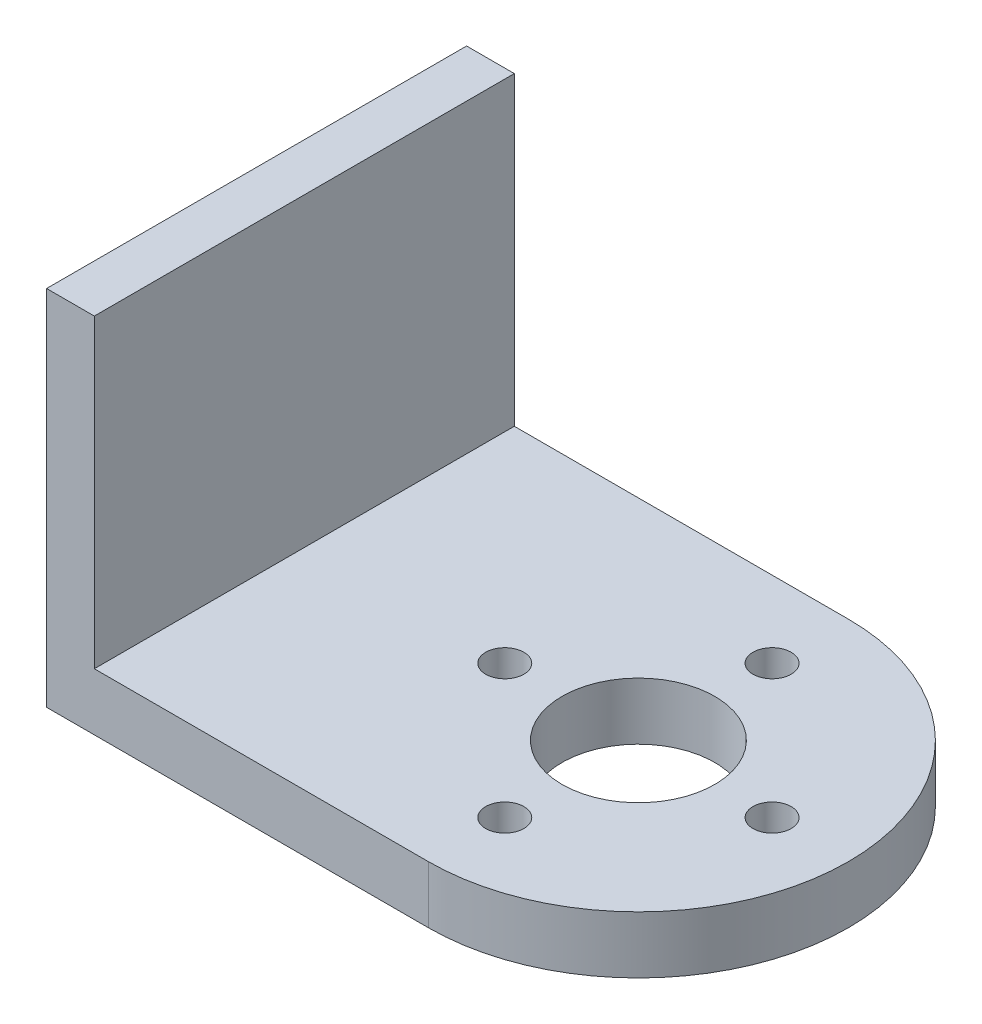
SolidWorks part; units mm, degrees
ref_plane "Front Plane" through (0, 0, 0) normal (0, 0, 1) x (1, 0, 0)
ref_plane "Top Plane" through (0, 0, 0) normal (0, 1, 0) x (1, 0, 0)
ref_plane "Right Plane" through (0, 0, 0) normal (1, 0, 0) x (0, 0, -1)
sketch "Sketch1" plane through (0, 0, 0) normal (0, 1, 0) x (1, 0, 0)
  line L0 (-28.2208, 0) -> (26.2745, 0) construction
  line L2 (-14, -11) -> (-14, 11)
  line L5 (-14, 11) -> (6, 11)
  line L6 (6, -11) -> (-14, -11)
  circle A0 centre (6, -7) radius 1
  circle A1 centre (-1, 0) radius 1
  circle A2 centre (6, 0) radius 4
  arc A3 (6, -11) -> (6, 11) centre (6, 0) ccw
  circle A4 centre (13, 0) radius 1
  circle A5 centre (6, 7) radius 1
  point P0 (0, 0)
  point P6 (-14, 0)
  point P22 (6, 0)
  dimension "D3" = 8
  dimension "D5" = 22
  dimension "D6" = 4
  dimension "D12" = 2
  dimension "D2" = 22
  dimension "D4" = 20
  dimension "D11" = 7
extrude "Boss-Extrude1" add sketch "Sketch1" along normal blind 3
sketch "Sketch2" plane through (0, 3, 0) normal (0, 1, 0) x (1, 0, 0)
  line L0 (-14, 11) -> (-11.5, 11)
  line L1 (6, 11) -> (-14, 11) construction
  line L2 (-11.5, 11) -> (-11.5, -11)
  line L3 (-14, -11) -> (6, -11) construction
  line L4 (-11.5, -11) -> (-14, -11)
  line L5 (-14, 11) -> (-14, -11)
  dimension "D1" = 2.5
extrude "Boss-Extrude2" add sketch "Sketch2" along normal blind 16
sketch "Sketch3" plane through (-11.5, 0, 0) normal (1, 0, 0) x (0, 0, -1)
  line L0 (11, 19) -> (11, 3) construction
  line L1 (-11, 19) -> (11, 19) construction
  line L2 (-11, 19) -> (-11, 3) construction
  circle A0 centre (6.9, 16) radius 1.1324
  circle A1 centre (-6.9, 16) radius 1.131
  point P6 (11, 11)
  point P11 (-11, 11)
  dimension "D1" = 4.1
  dimension "D2" = 3
  dimension "D3" = 4.1
  dimension "D4" = 3
sketch "Sketch4" plane through (-14, 0, 0) normal (-1, 0, 0) x (0, 0, 1)
  line L0 (-11, 19) -> (-11, 0) construction
  line L1 (-11, 19) -> (11, 19) construction
  line L2 (0, 0) -> (0, 25.5189) construction
  circle A0 centre (2.75, 13.55) radius 1
  circle A1 centre (-2.75, 13.55) radius 1
  dimension "D3" = 2
  dimension "D1" = 13.75
  dimension "D2" = 5.45
